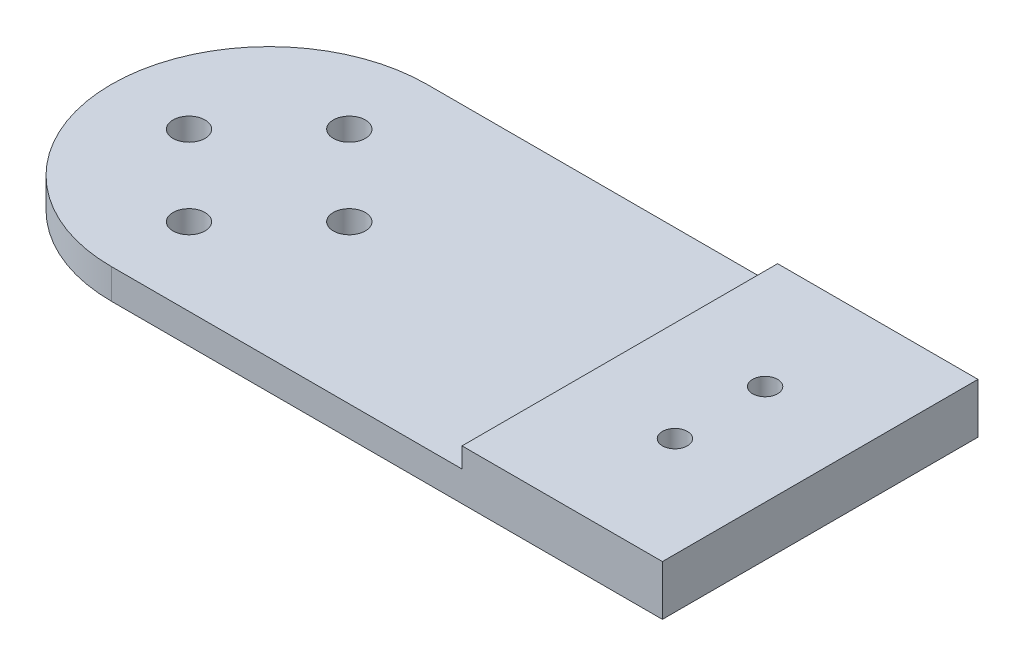
SolidWorks part; units mm, degrees
ref_plane "前视基准面" through (0, 0, 0) normal (0, 0, 1) x (1, 0, 0)
ref_plane "上视基准面" through (0, 0, 0) normal (0, 1, 0) x (1, 0, 0)
ref_plane "右视基准面" through (0, 0, 0) normal (1, 0, 0) x (0, 0, -1)
sketch "草图1" plane through (0, 0, 0) normal (0, 1, 0) x (1, 0, 0)
  line L0 (0, 0) -> (0, 12.2184) construction
  line L1 (0, 0) -> (14.977, 0) construction
  circle A0 centre (0, 0) radius 15.75
  circle A1 centre (0, 8) radius 1.6
  circle A2 centre (8, 0) radius 1.6
  circle A3 centre (0, -8) radius 1.6
  circle A4 centre (-8, 0) radius 1.6
  dimension "D1" = 31.5
  dimension "D4" = 3.2
  dimension "D5" = 3.2
  dimension "D2" = 8
  dimension "D3" = 8
extrude "凸台-拉伸1" add sketch "草图1" along normal blind 3
sketch "草图2" plane through (0, 0, 0) normal (0, -1, 0) x (1, 0, 0)
  line L1 (0, 15.75) -> (55, 15.75)
  line L3 (0, -15.75) -> (55, -15.75)
  line L4 (55, 15.75) -> (55, -15.75)
  circle A0 centre (0, 0) radius 15.75 construction
  arc A1 (0, -15.75) -> (0, 15.75) centre (0, 0) ccw
  dimension "D1" = 55
extrude "凸台-拉伸2" add sketch "草图2" against normal blind 3
sketch "草图3" plane through (0, 0, 0) normal (0, -1, 0) x (1, 0, 0)
  line L0 (0, -15.75) -> (55, -15.75) construction
  line L1 (55, 15.75) -> (35, 15.75)
  line L2 (55, 15.75) -> (55, -15.75)
  line L3 (55, -15.75) -> (35, -15.75)
  line L4 (35, 15.75) -> (35, -15.75)
  dimension "D1" = 20
extrude "凸台-拉伸3" add sketch "草图3" against normal blind 5
sketch "草图4" plane through (0, 5, 0) normal (0, 1, 0) x (1, 0, 0)
  circle A0 centre (45, 4.5) radius 1.25
  circle A1 centre (45, -4.5) radius 1.25
extrude "切除-拉伸1" cut sketch "草图4" against normal blind 10
